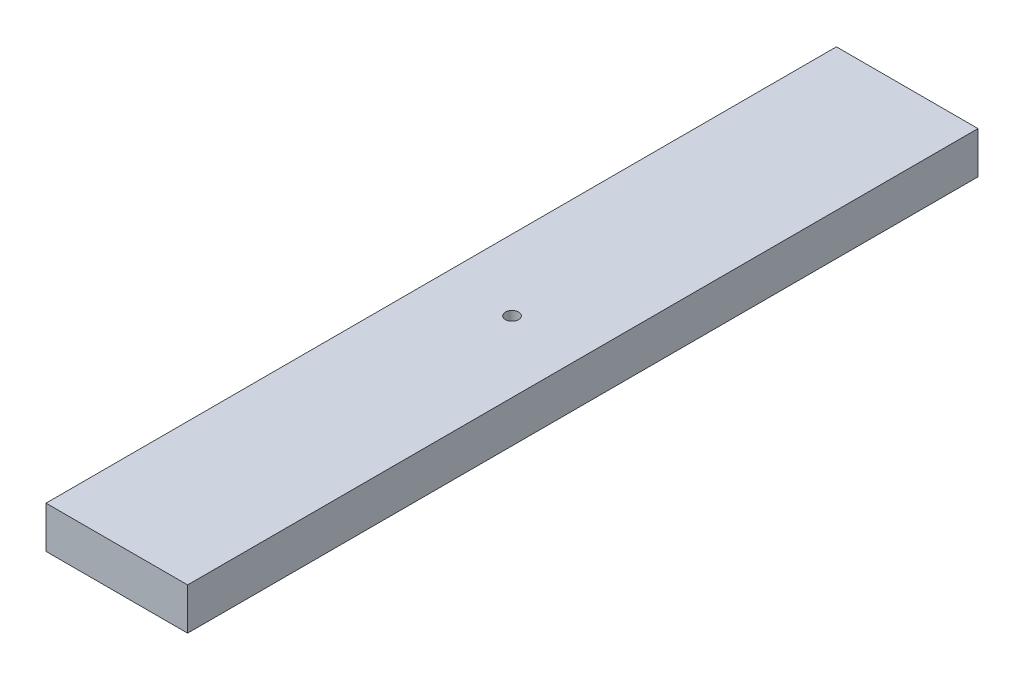
SolidWorks part; units mm, degrees
ref_plane "Front Plane" through (0, 0, 0) normal (0, 0, 1) x (1, 0, 0)
ref_plane "Top Plane" through (0, 0, 0) normal (0, 1, 0) x (1, 0, 0)
ref_plane "Right Plane" through (0, 0, 0) normal (1, 0, 0) x (0, 0, -1)
sketch "Sketch2" plane through (0, 0, 0) normal (0, 1, 0) x (1, 0, 0)
  line L1 (-10.75, -60) -> (10.75, -60)
  line L2 (-10.75, -60) -> (-10.75, 60)
  line L3 (-10.75, 60) -> (10.75, 60)
  line L4 (10.75, -60) -> (10.75, 60)
  line L5 (-10.75, -60) -> (10.75, 60) construction
  line L6 (-10.75, 60) -> (10.75, -60) construction
  circle A0 centre (0, 0) radius 1
  point P0 (0, 0)
  dimension "D1" = 2
  dimension "D2" = 120
  dimension "D3" = 21.5
extrude "Boss-Extrude1" add sketch "Sketch2" along normal blind 6.35
